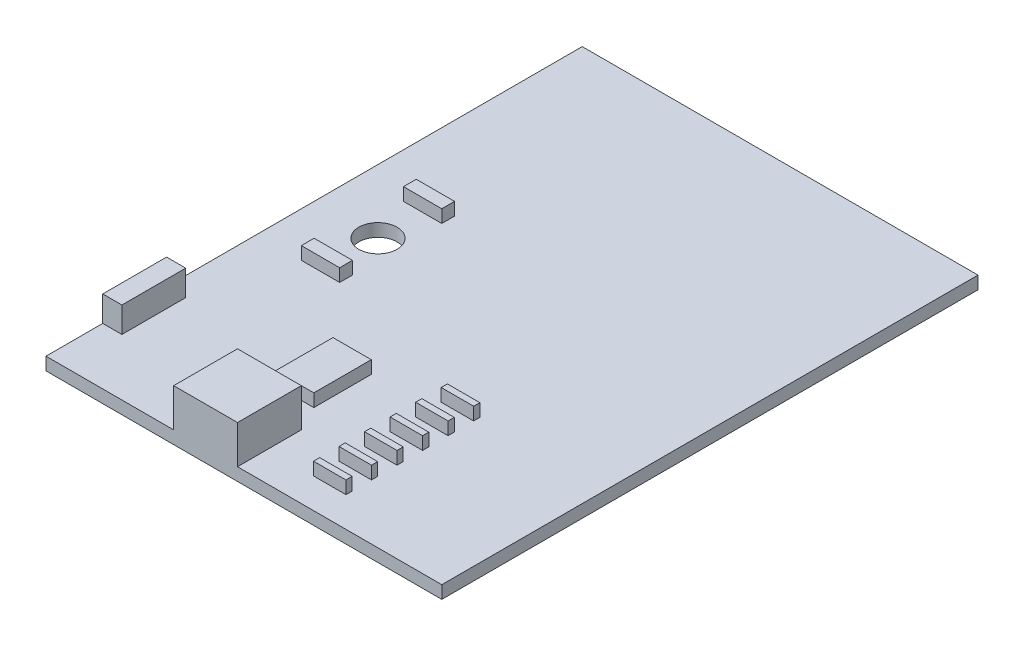
SolidWorks part; units mm, degrees
ref_plane "前基準面" through (0, 0, 0) normal (0, 0, 1) x (1, 0, 0)
ref_plane "上基準面" through (0, 0, 0) normal (0, 1, 0) x (1, 0, 0)
ref_plane "右基準面" through (0, 0, 0) normal (1, 0, 0) x (0, 0, -1)
sketch "草圖1" plane through (0, 0, 0) normal (0, 1, 0) x (1, 0, 0)
  line L0 (0, 21) -> (31, 21) construction
  line L1 (0, 0) -> (31, 0)
  line L2 (0, 0) -> (0, 42)
  line L3 (0, 42) -> (31, 42)
  line L4 (31, 0) -> (31, 42)
  line L6 (11.3458, 0) -> (16.3458, 0)
  circle A0 centre (5, 21) radius 1.5
  dimension "D3" = 3
  dimension "D4" = 5
  dimension "D1" = 31
  dimension "D2" = 42
extrude "填料-伸長1" add sketch "草圖1" along normal blind 1
sketch "草圖2" plane through (0, 1, 0) normal (0, 1, 0) x (1, 0, 0)
  line L0 (0, 0) -> (31, 0) construction
  line L1 (10, 0) -> (15, 0)
  line L2 (10, 0) -> (10, 5)
  line L3 (10, 5) -> (15, 5)
  line L4 (15, 0) -> (15, 5)
  circle A0 centre (5, 21) radius 1.5 construction
  dimension "D1" = 5
  dimension "D2" = 5
  dimension "D3" = 5
extrude "填料-伸長2" add sketch "草圖2" along normal blind 3
sketch "草圖3" plane through (0, 1, 0) normal (0, 1, 0) x (1, 0, 0)
  line L0 (15, 5) -> (10, 5) construction
  line L1 (10.9764, 11.5) -> (13.9764, 11.5)
  line L2 (10.9764, 11.5) -> (10.9764, 7)
  line L3 (10.9764, 7) -> (13.9764, 7)
  line L4 (13.9764, 11.5) -> (13.9764, 7)
  line L5 (18.6008, 12.838) -> (21.1423, 12.838)
  line L6 (18.6008, 12.838) -> (18.6008, 12.3522)
  line L7 (18.6008, 12.3522) -> (21.1423, 12.3522)
  line L8 (21.1423, 12.838) -> (21.1423, 12.3522)
  line L9 (19.8715, 12.3522) -> (19.8715, -2.0722) construction
  line L10 (18.6008, 10.838) -> (21.1423, 10.838)
  line L11 (18.6008, 10.3522) -> (21.1423, 10.3522)
  line L12 (18.6008, 10.838) -> (18.6008, 10.3522)
  line L13 (21.1423, 10.838) -> (21.1423, 10.3522)
  line L14 (18.6008, 8.838) -> (21.1423, 8.838)
  line L15 (18.6008, 8.3522) -> (21.1423, 8.3522)
  line L16 (18.6008, 8.838) -> (18.6008, 8.3522)
  line L17 (21.1423, 8.838) -> (21.1423, 8.3522)
  line L18 (18.6008, 6.838) -> (21.1423, 6.838)
  line L19 (18.6008, 6.3522) -> (21.1423, 6.3522)
  line L20 (18.6008, 6.838) -> (18.6008, 6.3522)
  line L21 (21.1423, 6.838) -> (21.1423, 6.3522)
  line L22 (18.6008, 4.838) -> (21.1423, 4.838)
  line L23 (18.6008, 4.3522) -> (21.1423, 4.3522)
  line L24 (18.6008, 4.838) -> (18.6008, 4.3522)
  line L25 (21.1423, 4.838) -> (21.1423, 4.3522)
  line L26 (18.6008, 2.838) -> (21.1423, 2.838)
  line L27 (18.6008, 2.3522) -> (21.1423, 2.3522)
  line L28 (18.6008, 2.838) -> (18.6008, 2.3522)
  line L29 (21.1423, 2.838) -> (21.1423, 2.3522)
  dimension "D1" = 3
  dimension "D2" = 4.5
  dimension "D3" = 2
  dimension "D4" = 6
extrude "填料-伸長3" add sketch "草圖3" along normal blind 1
sketch "草圖4" plane through (0, 1, 0) normal (0, 1, 0) x (1, 0, 0)
  line L0 (5, 21) -> (5, 15.9608) construction
  line L1 (3.5, 25.5) -> (6.5, 25.5)
  line L2 (3.5, 25.5) -> (3.5, 24.5)
  line L3 (3.5, 24.5) -> (6.5, 24.5)
  line L4 (6.5, 25.5) -> (6.5, 24.5)
  line L9 (5, 21) -> (-2.1674, 21) construction
  line L10 (3.5, 17.5) -> (6.5, 17.5)
  line L11 (6.5, 16.5) -> (6.5, 17.5)
  line L12 (3.5, 16.5) -> (6.5, 16.5)
  line L13 (3.5, 16.5) -> (3.5, 17.5)
  circle A0 centre (5, 21) radius 1.5 construction
  dimension "D3" = 1.5
  dimension "D1" = 3
  dimension "D2" = 1
  dimension "D4" = 3.5
extrude "填料-伸長4" add sketch "草圖4" along normal blind 1
sketch "草圖5" plane through (0, 1, 0) normal (0, 1, 0) x (1, 0, 0)
  line L0 (0, 0) -> (0, 42) construction
  line L1 (0, 9.4446) -> (1.5, 9.4446)
  line L2 (0, 9.4446) -> (0, 4.4446)
  line L3 (0, 4.4446) -> (1.5, 4.4446)
  line L4 (1.5, 9.4446) -> (1.5, 4.4446)
  dimension "D1" = 5
  dimension "D2" = 1.5
extrude "填料-伸長5" add sketch "草圖5" along normal blind 2
